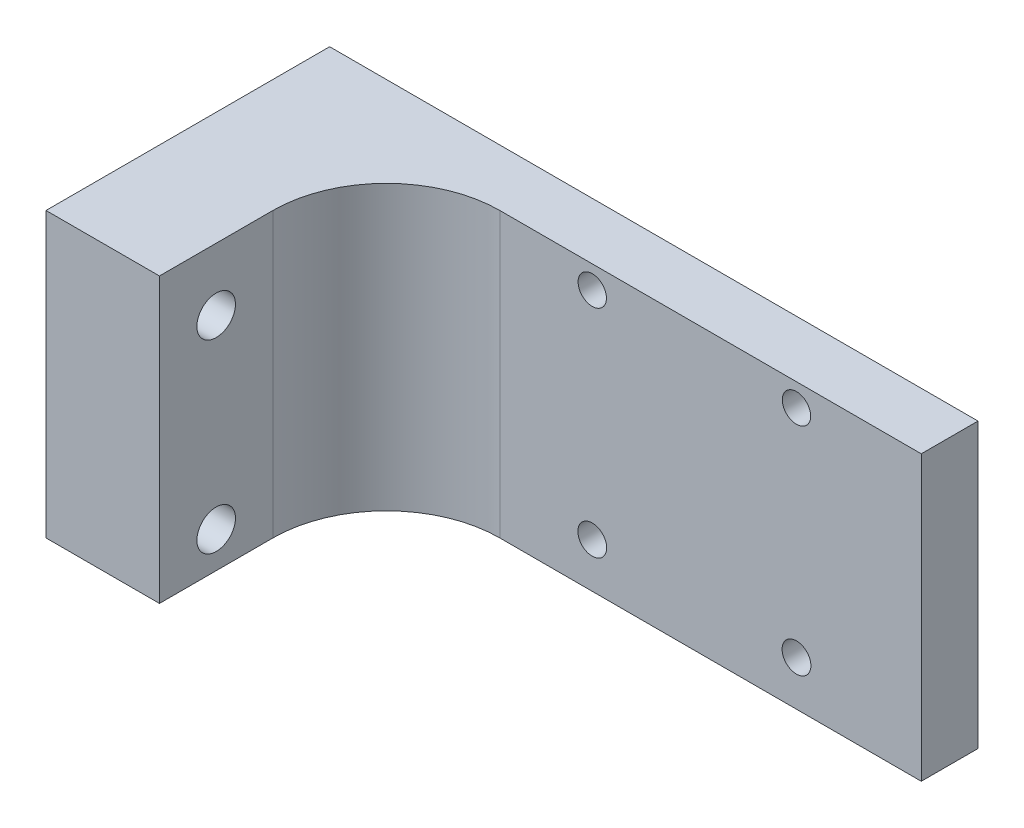
SolidWorks part; units mm, degrees
ref_plane "Front Plane" through (0, 0, 0) normal (0, 0, 1) x (1, 0, 0)
ref_plane "Top Plane" through (0, 0, 0) normal (0, 1, 0) x (1, 0, 0)
ref_plane "Right Plane" through (0, 0, 0) normal (1, 0, 0) x (0, 0, -1)
sketch "Sketch1" plane through (0, 0, 0) normal (0, 0, 1) x (1, 0, 0)
  line L1 (0, 0) -> (57.15, 0)
  line L2 (0, 0) -> (0, -25)
  line L3 (0, -25) -> (57.15, -25)
  line L4 (57.15, 0) -> (57.15, -25)
  dimension "D1" = 57.15
  dimension "D2" = 25
extrude "Boss-Extrude1" add sketch "Sketch1" along normal blind 5
sketch "Sketch2" plane through (0, 0, 5) normal (0, 0, 1) x (1, 0, 0)
  line L0 (0, -2) -> (57.15, -2) construction
  line L1 (0, 0) -> (0, -25) construction
  line L2 (57.15, -25) -> (57.15, 0) construction
  line L3 (37.15, -25) -> (37.15, 0) construction
  line L4 (28.15, -2) -> (28.15, -25) construction
  line L5 (46.15, -2) -> (46.15, -25) construction
  line L6 (17.15, -25) -> (17.15, 0) construction
  line L7 (0, -25) -> (57.15, -25) construction
  line L8 (57.15, 0) -> (0, 0) construction
  line L9 (57.15, -25) -> (57.15, 0) construction
  circle A2 centre (28.15, -2) radius 1.25
  circle A3 centre (46.15, -2) radius 1.25
  circle A4 centre (28.15, -21.05) radius 1.27
  circle A5 centre (46.15, -21.05) radius 1.27
  dimension "D3" = 9
  dimension "D4" = 9
  dimension "D2" = 20
  dimension "D7" = 2.5
  dimension "D8" = 2.54
  dimension "D9" = 19.05
  dimension "D1" = 2
  dimension "D5" = 19.05
  dimension "D6" = 40
extrude "Cut-Extrude2" cut sketch "Sketch2" against normal through all
sketch "Sketch5" plane through (0, 0, 5) normal (0, 0, 1) x (1, 0, 0)
  line L0 (10, 0) -> (10, -25) construction
  line L1 (57.15, 0) -> (0, 0) construction
  line L2 (0, -25) -> (57.15, -25) construction
  line L4 (0, 0) -> (10, 0)
  line L5 (0, 0) -> (0, -25)
  line L6 (0, -25) -> (10, -25)
  line L7 (10, 0) -> (10, -25)
  dimension "D1" = 10
extrude "Boss-Extrude3" add sketch "Sketch5" along normal blind 20
fillet "Fillet1" radius 10 1 edges at (10, -12.5, 5)
sketch "Sketch6" plane through (10, 0, 0) normal (1, 0, 0) x (0, 0, -1)
  line L0 (-20, -25) -> (-20, 0) construction
  line L1 (-25, -25) -> (-15, -25) construction
  line L2 (-25, 0) -> (-15, 0) construction
  circle A0 centre (-20, -21.8349) radius 1.7
  circle A1 centre (-20, -5.5031) radius 1.7
extrude "Cut-Extrude3" cut sketch "Sketch6" against normal through all
